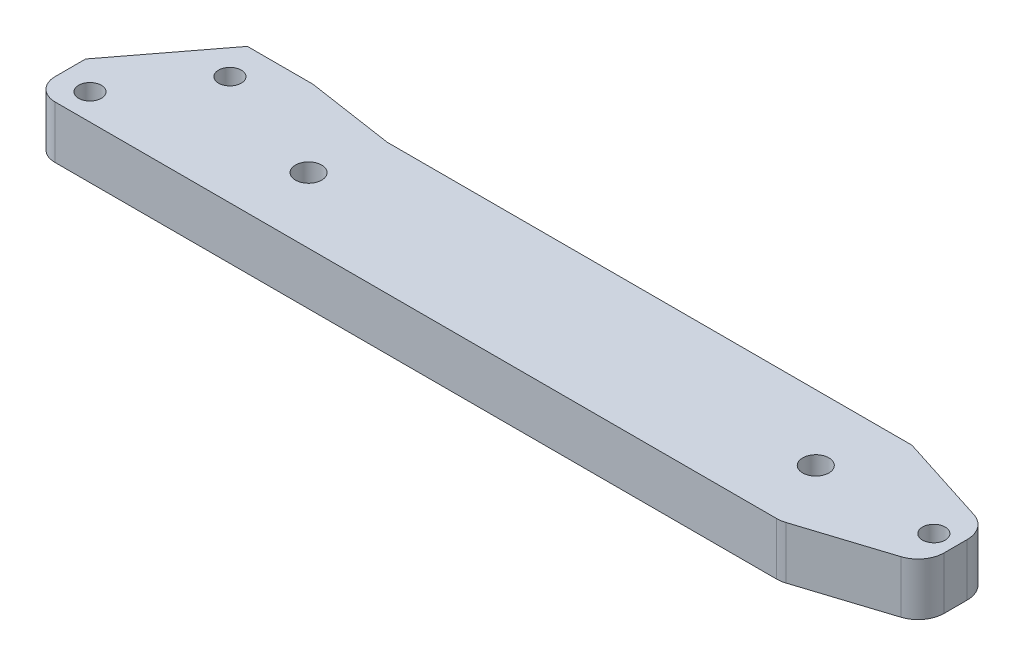
SolidWorks part; units mm, degrees
material "ABS"
ref_plane "Front Plane" through (0, 0, 0) normal (0, 0, 1) x (1, 0, 0)
ref_plane "Top Plane" through (0, 0, 0) normal (0, 1, 0) x (1, 0, 0)
ref_plane "Right Plane" through (0, 0, 0) normal (1, 0, 0) x (0, 0, -1)
sketch "Sketch1" plane through (0, 0, 0) normal (0, 1, 0) x (1, 0, 0)
  line L0 (180, 22) -> (155, 30)
  line L5 (180, 8) -> (155, 0)
  line L7 (-16, 12) -> (-16, 0)
  line L8 (-16, 0) -> (0, 0)
  line L9 (0, 0) -> (155, 0)
  line L10 (180, 8) -> (180, 22)
  line L12 (-16, 12) -> (0, 33)
  line L13 (0, 33) -> (15, 33)
  line L14 (15, 33) -> (35, 30)
  line L15 (35, 30) -> (155, 30)
  circle A0 centre (-9, 6) radius 2.6
  circle A1 centre (148, 15) radius 3
  circle A2 centre (32, 15) radius 3
  circle A3 centre (175, 15) radius 2.6
  circle A4 centre (4, 25) radius 2.6
  dimension "D9" = 5.2
  dimension "D12" = 6
  dimension "D15" = 6
  dimension "D13" = 5.2
  dimension "D17" = 19
  dimension "D20" = 15
  dimension "D14" = 5.2
  dimension "D3" = 4
  dimension "D4" = 8
  dimension "D5" = 25
  dimension "D6" = 25
  dimension "D7" = 16
  dimension "D8" = 12
  dimension "D10" = 7
  dimension "D11" = 6
  dimension "D16" = 5
  dimension "D19" = 33
  dimension "D21" = 20
extrude "Boss-Extrude1" add sketch "Sketch1" along normal blind 12
fillet "Fillet1" radius 5 1 edges at (-16, 6, 0)
fillet "Fillet2" radius 6 3 edges at (155, 6, 0) (180, 6, -8) (180, 6, -22)
